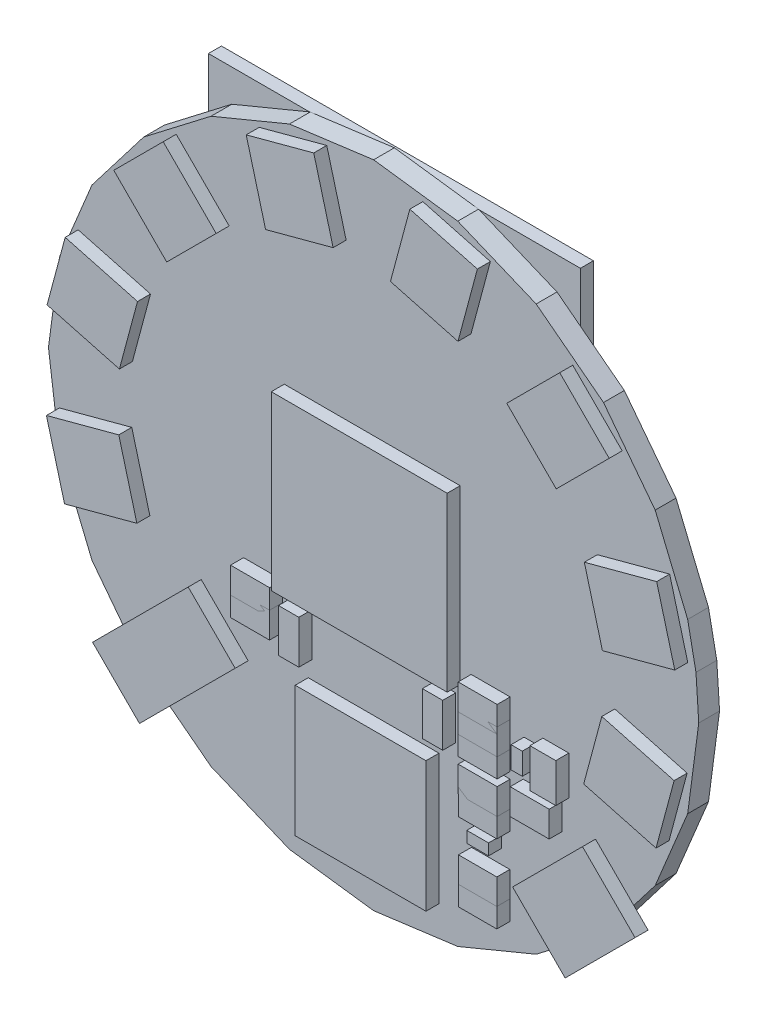
SolidWorks part; units mm, degrees
ref_plane "Plan de face" through (0, 0, 0) normal (0, 0, 1) x (1, 0, 0)
ref_plane "Plan de dessus" through (0, 0, 0) normal (0, 1, 0) x (1, 0, 0)
ref_plane "Plan de droite" through (0, 0, 0) normal (1, 0, 0) x (0, 0, -1)
sketch "Esquisse1" plane through (0, 0, 0) normal (0, 0, 1) x (1, 0, 0)
  line L0 (140.8, 53.6) -> (140.5861, 56.8632)
  line L1 (140.5861, 56.8632) -> (139.9481, 60.0705)
  line L2 (139.9481, 60.0705) -> (137.4506, 66.1)
  line L3 (137.4506, 66.1) -> (133.4777, 71.2777)
  line L4 (133.4777, 71.2777) -> (128.3, 75.2506)
  line L5 (128.3, 75.2506) -> (122.2705, 77.7481)
  line L6 (122.2705, 77.7481) -> (115.8, 78.6)
  line L7 (115.8, 78.6) -> (109.3295, 77.7481)
  line L8 (109.3295, 77.7481) -> (103.3, 75.2506)
  line L9 (103.3, 75.2506) -> (98.1223, 71.2777)
  line L10 (98.1223, 71.2777) -> (94.1494, 66.1)
  line L11 (94.1494, 66.1) -> (91.6519, 60.0705)
  line L12 (91.6519, 60.0705) -> (90.8, 53.6)
  line L13 (90.8, 53.6) -> (91.6519, 47.1295)
  line L14 (91.6519, 47.1295) -> (94.1494, 41.1)
  line L15 (94.1494, 41.1) -> (98.1223, 35.9223)
  line L16 (98.1223, 35.9223) -> (103.3, 31.9494)
  line L17 (103.3, 31.9494) -> (109.3295, 29.4519)
  line L18 (109.3295, 29.4519) -> (115.8, 28.6)
  line L19 (115.8, 28.6) -> (122.2705, 29.4519)
  line L20 (122.2705, 29.4519) -> (128.3, 31.9494)
  line L21 (128.3, 31.9494) -> (133.4777, 35.9223)
  line L22 (133.4777, 35.9223) -> (137.4506, 41.1)
  line L23 (137.4506, 41.1) -> (139.9481, 47.1295)
  line L24 (139.9481, 47.1295) -> (140.8, 53.6)
extrude "BOARD" add sketch "Esquisse1" along normal blind 1.6 separate body
ref_plane "Plan1" through (0, 0, 1.6) normal (0, 0, 1) x (1, 0, 0)
sketch "Esquisse2" plane through (0, 0, 1.6) normal (0, 0, 1) x (1, 0, 0)
  line L0 (91.6447, 49.9981) -> (97.2062, 51.4883)
  line L1 (97.2062, 51.4883) -> (98.5977, 46.2952)
  line L2 (98.5977, 46.2952) -> (93.0362, 44.805)
  line L3 (93.0362, 44.805) -> (91.6447, 49.9981)
extrude "WS2812B-1" add sketch "Esquisse2" along normal blind 1 separate body
sketch "Esquisse3" plane through (0, 0, 1.6) normal (0, 0, 1) x (1, 0, 0)
  line L0 (93.0853, 62.5782) -> (98.6468, 61.088)
  line L1 (98.6468, 61.088) -> (97.2553, 55.8949)
  line L2 (97.2553, 55.8949) -> (91.6938, 57.3851)
  line L3 (91.6938, 57.3851) -> (93.0853, 62.5782)
extrude "WS2812B-2" add sketch "Esquisse3" along normal blind 1 separate body
sketch "Esquisse4" plane through (0, 0, 1.6) normal (0, 0, 1) x (1, 0, 0)
  line L0 (100.6229, 72.7129) -> (104.6942, 68.6416)
  line L1 (104.6942, 68.6416) -> (100.8925, 64.8399)
  line L2 (100.8925, 64.8399) -> (96.8212, 68.9112)
  line L3 (96.8212, 68.9112) -> (100.6229, 72.7129)
extrude "WS2812B-3" add sketch "Esquisse4" along normal blind 1 separate body
sketch "Esquisse5" plane through (0, 0, 1.6) normal (0, 0, 1) x (1, 0, 0)
  line L0 (112.1981, 77.7553) -> (113.6883, 72.1938)
  line L1 (113.6883, 72.1938) -> (108.4952, 70.8023)
  line L2 (108.4952, 70.8023) -> (107.005, 76.3638)
  line L3 (107.005, 76.3638) -> (112.1981, 77.7553)
extrude "WS2812B-4" add sketch "Esquisse5" along normal blind 1 separate body
sketch "Esquisse6" plane through (0, 0, 1.6) normal (0, 0, 1) x (1, 0, 0)
  line L0 (124.7782, 76.3147) -> (123.288, 70.7532)
  line L1 (123.288, 70.7532) -> (118.0949, 72.1447)
  line L2 (118.0949, 72.1447) -> (119.5851, 77.7062)
  line L3 (119.5851, 77.7062) -> (124.7782, 76.3147)
extrude "WS2812B-5" add sketch "Esquisse6" along normal blind 1 separate body
sketch "Esquisse7" plane through (0, 0, 1.6) normal (0, 0, 1) x (1, 0, 0)
  line L0 (134.9129, 68.7771) -> (130.8416, 64.7058)
  line L1 (130.8416, 64.7058) -> (127.0399, 68.5075)
  line L2 (127.0399, 68.5075) -> (131.1112, 72.5788)
  line L3 (131.1112, 72.5788) -> (134.9129, 68.7771)
extrude "WS2812B-6" add sketch "Esquisse7" along normal blind 1 separate body
sketch "Esquisse8" plane through (0, 0, 1.6) normal (0, 0, 1) x (1, 0, 0)
  line L0 (139.9553, 57.2019) -> (134.3938, 55.7117)
  line L1 (134.3938, 55.7117) -> (133.0023, 60.9048)
  line L2 (133.0023, 60.9048) -> (138.5638, 62.395)
  line L3 (138.5638, 62.395) -> (139.9553, 57.2019)
extrude "WS2812B-7" add sketch "Esquisse8" along normal blind 1 separate body
sketch "Esquisse9" plane through (0, 0, 1.6) normal (0, 0, 1) x (1, 0, 0)
  line L0 (138.5147, 44.6218) -> (132.9532, 46.112)
  line L1 (132.9532, 46.112) -> (134.3447, 51.3051)
  line L2 (134.3447, 51.3051) -> (139.9062, 49.8149)
  line L3 (139.9062, 49.8149) -> (138.5147, 44.6218)
extrude "WS2812B-8" add sketch "Esquisse9" along normal blind 1 separate body
sketch "Esquisse10" plane through (0, 0, 0) normal (0, 0, 1) x (1, 0, 0)
  line L0 (130.1, 77.727) -> (101.5, 77.727)
  line L1 (101.5, 77.727) -> (101.5, 57.473)
  line L2 (101.5, 57.473) -> (130.1, 57.473)
  line L3 (130.1, 57.473) -> (130.1, 77.727)
extrude "3V_BAT_HOLDER-1" add sketch "Esquisse10" against normal blind 1 separate body
sketch "Esquisse11" plane through (0, 0, 1.6) normal (0, 0, 1) x (1, 0, 0)
  line L0 (123.3016, 42.6084) -> (126.2984, 42.6084)
  line L1 (126.2984, 42.6084) -> (126.2984, 40.617)
  line L2 (126.2984, 40.617) -> (123.3016, 40.617)
  line L3 (123.3016, 40.617) -> (123.3016, 42.6084)
extrude "C0603-1" add sketch "Esquisse11" along normal blind 1 separate body
sketch "Esquisse12" plane through (0, 0, 1.6) normal (0, 0, 1) x (1, 0, 0)
  line L0 (127.3016, 43.1084) -> (130.2984, 43.1084)
  line L1 (130.2984, 43.1084) -> (130.2984, 41.117)
  line L2 (130.2984, 41.117) -> (127.3016, 41.117)
  line L3 (127.3016, 41.117) -> (127.3016, 43.1084)
extrude "C0603-2" add sketch "Esquisse12" along normal blind 1 separate body
sketch "Esquisse13" plane through (0, 0, 1.6) normal (0, 0, 1) x (1, 0, 0)
  line L0 (123.3016, 45.1084) -> (126.2984, 45.1084)
  line L1 (126.2984, 45.1084) -> (126.2984, 43.117)
  line L2 (126.2984, 43.117) -> (123.3016, 43.117)
  line L3 (123.3016, 43.117) -> (123.3016, 45.1084)
extrude "C0603-3" add sketch "Esquisse13" along normal blind 1 separate body
sketch "Esquisse14" plane through (0, 0, 1.6) normal (0, 0, 1) x (1, 0, 0)
  line L0 (105.8016, 45.6084) -> (108.7984, 45.6084)
  line L1 (108.7984, 45.6084) -> (108.7984, 43.617)
  line L2 (108.7984, 43.617) -> (105.8016, 43.617)
  line L3 (105.8016, 43.617) -> (105.8016, 45.6084)
extrude "C0603-4" add sketch "Esquisse14" along normal blind 1 separate body
sketch "Esquisse15" plane through (0, 0, 1.6) normal (0, 0, 1) x (1, 0, 0)
  line L0 (130.8084, 46.5984) -> (130.8084, 43.6016)
  line L1 (130.8084, 43.6016) -> (128.817, 43.6016)
  line L2 (128.817, 43.6016) -> (128.817, 46.5984)
  line L3 (128.817, 46.5984) -> (130.8084, 46.5984)
extrude "C0603-5" add sketch "Esquisse15" along normal blind 1 separate body
sketch "Esquisse16" plane through (0, 0, 1.6) normal (0, 0, 1) x (1, 0, 0)
  line L0 (126.2984, 44.5916) -> (123.3016, 44.5916)
  line L1 (123.3016, 44.5916) -> (123.3016, 46.583)
  line L2 (123.3016, 46.583) -> (126.2984, 46.583)
  line L3 (126.2984, 46.583) -> (126.2984, 44.5916)
extrude "C0603-6" add sketch "Esquisse16" along normal blind 1 separate body
sketch "Esquisse17" plane through (0, 0, 1.6) normal (0, 0, 1) x (1, 0, 0)
  line L0 (105.8016, 47.1084) -> (108.7984, 47.1084)
  line L1 (108.7984, 47.1084) -> (108.7984, 45.117)
  line L2 (108.7984, 45.117) -> (105.8016, 45.117)
  line L3 (105.8016, 45.117) -> (105.8016, 47.1084)
extrude "C0603-7" add sketch "Esquisse17" along normal blind 1 separate body
sketch "Esquisse18" plane through (0, 0, 1.6) normal (0, 0, 1) x (1, 0, 0)
  line L0 (126.2984, 46.0916) -> (123.3016, 46.0916)
  line L1 (123.3016, 46.0916) -> (123.3016, 48.083)
  line L2 (123.3016, 48.083) -> (126.2984, 48.083)
  line L3 (126.2984, 48.083) -> (126.2984, 46.0916)
extrude "C0603-8" add sketch "Esquisse18" along normal blind 1 separate body
sketch "Esquisse19" plane through (0, 0, 0) normal (0, 0, 1) x (1, 0, 0)
  line L0 (130.8856, 42.8738) -> (132.7279, 42.8738)
  line L1 (132.7279, 42.8738) -> (132.7279, 44.3239)
  line L2 (132.7279, 44.3239) -> (130.8856, 44.3239)
  line L3 (130.8856, 44.3239) -> (130.8856, 42.8738)
extrude "C0805POL-1" add sketch "Esquisse19" against normal blind 1 separate body
sketch "Esquisse20" plane through (0, 0, 0) normal (0, 0, 1) x (1, 0, 0)
  line L0 (100.6916, 45.9984) -> (100.6916, 42.0016)
  line L1 (100.6916, 42.0016) -> (102.683, 42.0016)
  line L2 (102.683, 42.0016) -> (102.683, 45.9984)
  line L3 (102.683, 45.9984) -> (100.6916, 45.9984)
extrude "C0805-1" add sketch "Esquisse20" against normal blind 1 separate body
sketch "Esquisse21" plane through (0, 0, 0) normal (0, 0, 1) x (1, 0, 0)
  line L0 (99.5984, 45.6084) -> (95.6016, 45.6084)
  line L1 (95.6016, 45.6084) -> (95.6016, 43.617)
  line L2 (95.6016, 43.617) -> (99.5984, 43.617)
  line L3 (99.5984, 43.617) -> (99.5984, 45.6084)
extrude "C0805-2" add sketch "Esquisse21" against normal blind 1 separate body
sketch "Esquisse22" plane through (0, 0, 0) normal (0, 0, 1) x (1, 0, 0)
  line L0 (135.8084, 44.6016) -> (135.8084, 47.5984)
  line L1 (135.8084, 47.5984) -> (133.817, 47.5984)
  line L2 (133.817, 47.5984) -> (133.817, 44.6016)
  line L3 (133.817, 44.6016) -> (135.8084, 44.6016)
extrude "C0603-9" add sketch "Esquisse22" against normal blind 1 separate body
sketch "Esquisse23" plane through (0, 0, 0) normal (0, 0, 1) x (1, 0, 0)
  line L0 (111.8084, 45.6016) -> (111.8084, 48.5984)
  line L1 (111.8084, 48.5984) -> (109.817, 48.5984)
  line L2 (109.817, 48.5984) -> (109.817, 45.6016)
  line L3 (109.817, 45.6016) -> (111.8084, 45.6016)
extrude "C0603-10" add sketch "Esquisse23" against normal blind 1 separate body
sketch "Esquisse24" plane through (0, 0, 0) normal (0, 0, 1) x (1, 0, 0)
  line L0 (121.8084, 45.6016) -> (121.8084, 48.5984)
  line L1 (121.8084, 48.5984) -> (119.817, 48.5984)
  line L2 (119.817, 48.5984) -> (119.817, 45.6016)
  line L3 (119.817, 45.6016) -> (121.8084, 45.6016)
extrude "C0603-11" add sketch "Esquisse24" against normal blind 1 separate body
sketch "Esquisse25" plane through (0, 0, 0) normal (0, 0, 1) x (1, 0, 0)
  line L0 (123.5738, 48.0144) -> (123.5738, 46.1721)
  line L1 (123.5738, 46.1721) -> (125.0239, 46.1721)
  line L2 (125.0239, 46.1721) -> (125.0239, 48.0144)
  line L3 (125.0239, 48.0144) -> (123.5738, 48.0144)
extrude "C0805POL-2" add sketch "Esquisse25" against normal blind 1 separate body
sketch "Esquisse26" plane through (0, 0, 0) normal (0, 0, 1) x (1, 0, 0)
  line L0 (98.5144, 49.3262) -> (96.6721, 49.3262)
  line L1 (96.6721, 49.3262) -> (96.6721, 47.8761)
  line L2 (96.6721, 47.8761) -> (98.5144, 47.8761)
  line L3 (98.5144, 47.8761) -> (98.5144, 49.3262)
extrude "C0805POL-3" add sketch "Esquisse26" against normal blind 1 separate body
sketch "Esquisse27" plane through (0, 0, 0) normal (0, 0, 1) x (1, 0, 0)
  line L0 (128.7144, 49.3262) -> (126.8721, 49.3262)
  line L1 (126.8721, 49.3262) -> (126.8721, 47.8761)
  line L2 (126.8721, 47.8761) -> (128.7144, 47.8761)
  line L3 (128.7144, 47.8761) -> (128.7144, 49.3262)
extrude "C0805POL-4" add sketch "Esquisse27" against normal blind 1 separate body
sketch "Esquisse28" plane through (0, 0, 0) normal (0, 0, 1) x (1, 0, 0)
  line L0 (128.7144, 51.8262) -> (126.8721, 51.8262)
  line L1 (126.8721, 51.8262) -> (126.8721, 50.3761)
  line L2 (126.8721, 50.3761) -> (128.7144, 50.3761)
  line L3 (128.7144, 50.3761) -> (128.7144, 51.8262)
extrude "C0805POL-5" add sketch "Esquisse28" against normal blind 1 separate body
sketch "Esquisse29" plane through (0, 0, 0) normal (0, 0, 1) x (1, 0, 0)
  line L0 (134.3016, 50.5916) -> (137.2984, 50.5916)
  line L1 (137.2984, 50.5916) -> (137.2984, 52.583)
  line L2 (137.2984, 52.583) -> (134.3016, 52.583)
  line L3 (134.3016, 52.583) -> (134.3016, 50.5916)
extrude "C0603-12" add sketch "Esquisse29" against normal blind 1 separate body
sketch "Esquisse30" plane through (0, 0, 0) normal (0, 0, 1) x (1, 0, 0)
  line L0 (128.7144, 54.3262) -> (126.8721, 54.3262)
  line L1 (126.8721, 54.3262) -> (126.8721, 52.8761)
  line L2 (126.8721, 52.8761) -> (128.7144, 52.8761)
  line L3 (128.7144, 52.8761) -> (128.7144, 54.3262)
extrude "C0805POL-6" add sketch "Esquisse30" against normal blind 1 separate body
sketch "Esquisse31" plane through (0, 0, 0) normal (0, 0, 1) x (1, 0, 0)
  line L0 (100.1916, 56.5984) -> (100.1916, 52.6016)
  line L1 (100.1916, 52.6016) -> (102.183, 52.6016)
  line L2 (102.183, 52.6016) -> (102.183, 56.5984)
  line L3 (102.183, 56.5984) -> (100.1916, 56.5984)
extrude "C0805-3" add sketch "Esquisse31" against normal blind 1 separate body
sketch "Esquisse32" plane through (0, 0, 0) normal (0, 0, 1) x (1, 0, 0)
  line L0 (102.2916, 56.5984) -> (102.2916, 52.6016)
  line L1 (102.2916, 52.6016) -> (104.283, 52.6016)
  line L2 (104.283, 52.6016) -> (104.283, 56.5984)
  line L3 (104.283, 56.5984) -> (102.2916, 56.5984)
extrude "C0805-4" add sketch "Esquisse32" against normal blind 1 separate body
sketch "Esquisse33" plane through (0, 0, 0) normal (0, 0, 1) x (1, 0, 0)
  line L0 (108.3084, 52.6016) -> (108.3084, 56.5984)
  line L1 (108.3084, 56.5984) -> (106.317, 56.5984)
  line L2 (106.317, 56.5984) -> (106.317, 52.6016)
  line L3 (106.317, 52.6016) -> (108.3084, 52.6016)
extrude "C0805-5" add sketch "Esquisse33" against normal blind 1 separate body
sketch "Esquisse34" plane through (0, 0, 0) normal (0, 0, 1) x (1, 0, 0)
  line L0 (135.5262, 53.6856) -> (135.5262, 55.5279)
  line L1 (135.5262, 55.5279) -> (134.0761, 55.5279)
  line L2 (134.0761, 55.5279) -> (134.0761, 53.6856)
  line L3 (134.0761, 53.6856) -> (135.5262, 53.6856)
extrude "C0805POL-7" add sketch "Esquisse34" against normal blind 1 separate body
sketch "Esquisse35" plane through (0, 0, 0) normal (0, 0, 1) x (1, 0, 0)
  line L0 (117.2916, 59.0984) -> (117.2916, 56.1016)
  line L1 (117.2916, 56.1016) -> (119.283, 56.1016)
  line L2 (119.283, 56.1016) -> (119.283, 59.0984)
  line L3 (119.283, 59.0984) -> (117.2916, 59.0984)
extrude "C0603-13" add sketch "Esquisse35" against normal blind 1 separate body
sketch "Esquisse36" plane through (0, 0, 0) normal (0, 0, 1) x (1, 0, 0)
  line L0 (125.3084, 56.1016) -> (125.3084, 59.0984)
  line L1 (125.3084, 59.0984) -> (123.317, 59.0984)
  line L2 (123.317, 59.0984) -> (123.317, 56.1016)
  line L3 (123.317, 56.1016) -> (125.3084, 56.1016)
extrude "C0603-14" add sketch "Esquisse36" against normal blind 1 separate body
sketch "Esquisse37" plane through (0, 0, 0) normal (0, 0, 1) x (1, 0, 0)
  line L0 (127.5738, 62.5144) -> (127.5738, 60.6721)
  line L1 (127.5738, 60.6721) -> (129.0239, 60.6721)
  line L2 (129.0239, 60.6721) -> (129.0239, 62.5144)
  line L3 (129.0239, 62.5144) -> (127.5738, 62.5144)
extrude "C0805POL-8" add sketch "Esquisse37" against normal blind 1 separate body
sketch "Esquisse38" plane through (0, 0, 0) normal (0, 0, 1) x (1, 0, 0)
  line L0 (134.2984, 63.6084) -> (129.3016, 63.6084)
  line L1 (129.3016, 63.6084) -> (129.3016, 61.617)
  line L2 (129.3016, 61.617) -> (134.2984, 61.617)
  line L3 (134.2984, 61.617) -> (134.2984, 63.6084)
extrude "C1206-1" add sketch "Esquisse38" against normal blind 1 separate body
sketch "Esquisse39" plane through (0, 0, 0) normal (0, 0, 1) x (1, 0, 0)
  line L0 (126.6, 45.3865) -> (129, 45.3865)
  line L1 (129, 45.3865) -> (129, 46.75)
  line L2 (129, 46.75) -> (126.6, 46.75)
  line L3 (126.6, 46.75) -> (126.6, 45.3865)
extrude "SOD-323F-1" add sketch "Esquisse39" against normal blind 1 separate body
sketch "Esquisse40" plane through (0, 0, 0) normal (0, 0, 1) x (1, 0, 0)
  line L0 (137, 50.3135) -> (134.6, 50.3135)
  line L1 (134.6, 50.3135) -> (134.6, 48.95)
  line L2 (134.6, 48.95) -> (137, 48.95)
  line L3 (137, 48.95) -> (137, 50.3135)
extrude "SOD-323F-2" add sketch "Esquisse40" against normal blind 1 separate body
sketch "Esquisse41" plane through (0, 0, 0) normal (0, 0, 1) x (1, 0, 0)
  line L0 (130.6, 54.8865) -> (133, 54.8865)
  line L1 (133, 54.8865) -> (133, 56.25)
  line L2 (133, 56.25) -> (130.6, 56.25)
  line L3 (130.6, 56.25) -> (130.6, 54.8865)
extrude "SOD-323F-3" add sketch "Esquisse41" against normal blind 1 separate body
sketch "Esquisse42" plane through (0, 0, 0) normal (0, 0, 1) x (1, 0, 0)
  line L0 (135.5135, 57.9) -> (135.5135, 60.3)
  line L1 (135.5135, 60.3) -> (134.15, 60.3)
  line L2 (134.15, 60.3) -> (134.15, 57.9)
  line L3 (134.15, 57.9) -> (135.5135, 57.9)
extrude "SOD-323F-4" add sketch "Esquisse42" against normal blind 1 separate body
sketch "Esquisse43" plane through (0, 0, 0) normal (0, 0, 1) x (1, 0, 0)
  line L0 (129.2984, 44.6084) -> (126.3016, 44.6084)
  line L1 (126.3016, 44.6084) -> (126.3016, 42.617)
  line L2 (126.3016, 42.617) -> (129.2984, 42.617)
  line L3 (129.2984, 42.617) -> (129.2984, 44.6084)
extrude "0603-1" add sketch "Esquisse43" against normal blind 1 separate body
sketch "Esquisse44" plane through (0, 0, 0) normal (0, 0, 1) x (1, 0, 0)
  line L0 (130.15, 57.6) -> (133.45, 57.6)
  line L1 (133.45, 57.6) -> (133.45, 60.6)
  line L2 (133.45, 60.6) -> (130.15, 60.6)
  line L3 (130.15, 60.6) -> (130.15, 57.6)
extrude "SOT23-5-1" add sketch "Esquisse44" against normal blind 1 separate body
sketch "Esquisse45" plane through (0, 0, 1.6) normal (0, 0, 1) x (1, 0, 0)
  line L0 (95.1926, 36.6718) -> (102.5465, 44.0258)
  line L1 (102.5465, 44.0258) -> (106.1539, 40.4184)
  line L2 (106.1539, 40.4184) -> (98.8, 33.0645)
  line L3 (98.8, 33.0645) -> (95.1926, 36.6718)
extrude "STEREOJACK2_5MM-1" add sketch "Esquisse45" along normal blind 1 separate body
sketch "Esquisse46" plane through (0, 0, 0) normal (0, 0, 1) x (1, 0, 0)
  line L0 (112.2, 33) -> (119.4, 33)
  line L1 (119.4, 33) -> (119.4, 40.2)
  line L2 (119.4, 40.2) -> (112.2, 40.2)
  line L3 (112.2, 40.2) -> (112.2, 33)
extrude "LQFP32-08-1" add sketch "Esquisse46" against normal blind 1 separate body
sketch "Esquisse47" plane through (0, 0, 1.6) normal (0, 0, 1) x (1, 0, 0)
  line L0 (123.9618, 38.5318) -> (125.6382, 38.5318)
  line L1 (125.6382, 38.5318) -> (125.6382, 37.6678)
  line L2 (125.6382, 37.6678) -> (123.9618, 37.6678)
  line L3 (123.9618, 37.6678) -> (123.9618, 38.5318)
extrude "L0603-1" add sketch "Esquisse47" along normal blind 1 separate body
sketch "Esquisse48" plane through (0, 0, 1.6) normal (0, 0, 1) x (1, 0, 0)
  line L0 (127.3682, 44.2618) -> (127.3682, 45.9382)
  line L1 (127.3682, 45.9382) -> (128.2322, 45.9382)
  line L2 (128.2322, 45.9382) -> (128.2322, 44.2618)
  line L3 (128.2322, 44.2618) -> (127.3682, 44.2618)
extrude "L0603-2" add sketch "Esquisse48" along normal blind 1 separate body
sketch "Esquisse49" plane through (0, 0, 0) normal (0, 0, 1) x (1, 0, 0)
  line L0 (98.4382, 47.0318) -> (96.7618, 47.0318)
  line L1 (96.7618, 47.0318) -> (96.7618, 46.1678)
  line L2 (96.7618, 46.1678) -> (98.4382, 46.1678)
  line L3 (98.4382, 46.1678) -> (98.4382, 47.0318)
extrude "L0603-3" add sketch "Esquisse49" against normal blind 1 separate body
sketch "Esquisse50" plane through (0, 0, 0) normal (0, 0, 1) x (1, 0, 0)
  line L0 (98.4382, 51.0318) -> (96.7618, 51.0318)
  line L1 (96.7618, 51.0318) -> (96.7618, 50.1678)
  line L2 (96.7618, 50.1678) -> (98.4382, 50.1678)
  line L3 (98.4382, 50.1678) -> (98.4382, 51.0318)
extrude "L0603-4" add sketch "Esquisse50" against normal blind 1 separate body
sketch "Esquisse51" plane through (0, 0, 0) normal (0, 0, 1) x (1, 0, 0)
  line L0 (112.8682, 58.4382) -> (112.8682, 56.7618)
  line L1 (112.8682, 56.7618) -> (113.7322, 56.7618)
  line L2 (113.7322, 56.7618) -> (113.7322, 58.4382)
  line L3 (113.7322, 58.4382) -> (112.8682, 58.4382)
extrude "L0603-5" add sketch "Esquisse51" against normal blind 1 separate body
sketch "Esquisse52" plane through (0, 0, 0) normal (0, 0, 1) x (1, 0, 0)
  circle A0 centre (115.8, 53.6) radius 3
  dimension "D1" = 6
  dimension "D2" = 0
  dimension "D3" = 0
extrude "F6050AP-1" add sketch "Esquisse52" against normal blind 1 separate body
sketch "Esquisse53" plane through (0, 0, 0) normal (0, 0, 1) x (1, 0, 0)
  line L0 (102.7224, 62.8954) -> (99.8014, 62.8954)
  line L1 (99.8014, 62.8954) -> (99.8014, 60.3046)
  line L2 (99.8014, 60.3046) -> (102.7224, 60.3046)
  line L3 (102.7224, 60.3046) -> (102.7224, 62.8954)
extrude "SOT23-1" add sketch "Esquisse53" against normal blind 1 separate body
sketch "Esquisse54" plane through (0, 0, 1.6) normal (0, 0, 1) x (1, 0, 0)
  line L0 (123.327, 35.083) -> (126.273, 35.083)
  line L1 (126.273, 35.083) -> (126.273, 33.117)
  line L2 (126.273, 33.117) -> (123.327, 33.117)
  line L3 (123.327, 33.117) -> (123.327, 35.083)
extrude "R0603-1" add sketch "Esquisse54" along normal blind 1 separate body
sketch "Esquisse55" plane through (0, 0, 1.6) normal (0, 0, 1) x (1, 0, 0)
  line L0 (123.327, 36.583) -> (126.273, 36.583)
  line L1 (126.273, 36.583) -> (126.273, 34.617)
  line L2 (126.273, 34.617) -> (123.327, 34.617)
  line L3 (123.327, 34.617) -> (123.327, 36.583)
extrude "R0603-2" add sketch "Esquisse55" along normal blind 1 separate body
sketch "Esquisse56" plane through (0, 0, 1.6) normal (0, 0, 1) x (1, 0, 0)
  line L0 (123.327, 41.083) -> (126.273, 41.083)
  line L1 (126.273, 41.083) -> (126.273, 39.117)
  line L2 (126.273, 39.117) -> (123.327, 39.117)
  line L3 (123.327, 39.117) -> (123.327, 41.083)
extrude "R0603-3" add sketch "Esquisse56" along normal blind 1 separate body
sketch "Esquisse57" plane through (0, 0, 0) normal (0, 0, 1) x (1, 0, 0)
  line L0 (104.383, 33.927) -> (104.383, 36.873)
  line L1 (104.383, 36.873) -> (102.417, 36.873)
  line L2 (102.417, 36.873) -> (102.417, 33.927)
  line L3 (102.417, 33.927) -> (104.383, 33.927)
extrude "R0603-4" add sketch "Esquisse57" against normal blind 1 separate body
sketch "Esquisse58" plane through (0, 0, 0) normal (0, 0, 1) x (1, 0, 0)
  line L0 (106.183, 33.927) -> (106.183, 36.873)
  line L1 (106.183, 36.873) -> (104.217, 36.873)
  line L2 (104.217, 36.873) -> (104.217, 33.927)
  line L3 (104.217, 33.927) -> (106.183, 33.927)
extrude "R0603-5" add sketch "Esquisse58" against normal blind 1 separate body
sketch "Esquisse59" plane through (0, 0, 0) normal (0, 0, 1) x (1, 0, 0)
  line L0 (112.327, 47.117) -> (115.273, 47.117)
  line L1 (115.273, 47.117) -> (115.273, 49.083)
  line L2 (115.273, 49.083) -> (112.327, 49.083)
  line L3 (112.327, 49.083) -> (112.327, 47.117)
extrude "R0603-6" add sketch "Esquisse59" against normal blind 1 separate body
sketch "Esquisse60" plane through (0, 0, 0) normal (0, 0, 1) x (1, 0, 0)
  line L0 (119.273, 49.083) -> (116.327, 49.083)
  line L1 (116.327, 49.083) -> (116.327, 47.117)
  line L2 (116.327, 47.117) -> (119.273, 47.117)
  line L3 (119.273, 47.117) -> (119.273, 49.083)
extrude "R0603-7" add sketch "Esquisse60" against normal blind 1 separate body
sketch "Esquisse61" plane through (0, 0, 0) normal (0, 0, 1) x (1, 0, 0)
  line L0 (106.283, 53.127) -> (106.283, 56.073)
  line L1 (106.283, 56.073) -> (104.317, 56.073)
  line L2 (104.317, 56.073) -> (104.317, 53.127)
  line L3 (104.317, 53.127) -> (106.283, 53.127)
extrude "R0603-8" add sketch "Esquisse61" against normal blind 1 separate body
sketch "Esquisse62" plane through (0, 0, 0) normal (0, 0, 1) x (1, 0, 0)
  line L0 (135.817, 56.073) -> (135.817, 53.127)
  line L1 (135.817, 53.127) -> (137.783, 53.127)
  line L2 (137.783, 53.127) -> (137.783, 56.073)
  line L3 (137.783, 56.073) -> (135.817, 56.073)
extrude "R0603-9" add sketch "Esquisse62" against normal blind 1 separate body
sketch "Esquisse63" plane through (0, 0, 0) normal (0, 0, 1) x (1, 0, 0)
  line L0 (121.283, 56.127) -> (121.283, 59.073)
  line L1 (121.283, 59.073) -> (119.317, 59.073)
  line L2 (119.317, 59.073) -> (119.317, 56.127)
  line L3 (119.317, 56.127) -> (121.283, 56.127)
extrude "R0603-10" add sketch "Esquisse63" against normal blind 1 separate body
sketch "Esquisse64" plane through (0, 0, 0) normal (0, 0, 1) x (1, 0, 0)
  line L0 (121.317, 59.073) -> (121.317, 56.127)
  line L1 (121.317, 56.127) -> (123.283, 56.127)
  line L2 (123.283, 56.127) -> (123.283, 59.073)
  line L3 (123.283, 59.073) -> (121.317, 59.073)
extrude "R0603-11" add sketch "Esquisse64" against normal blind 1 separate body
sketch "Esquisse65" plane through (0, 0, 0) normal (0, 0, 1) x (1, 0, 0)
  line L0 (127.283, 56.127) -> (127.283, 59.073)
  line L1 (127.283, 59.073) -> (125.317, 59.073)
  line L2 (125.317, 59.073) -> (125.317, 56.127)
  line L3 (125.317, 56.127) -> (127.283, 56.127)
extrude "R0603-12" add sketch "Esquisse65" against normal blind 1 separate body
sketch "Esquisse66" plane through (0, 0, 0) normal (0, 0, 1) x (1, 0, 0)
  line L0 (127.317, 59.073) -> (127.317, 56.127)
  line L1 (127.317, 56.127) -> (129.283, 56.127)
  line L2 (129.283, 56.127) -> (129.283, 59.073)
  line L3 (129.283, 59.073) -> (127.317, 59.073)
extrude "R0603-13" add sketch "Esquisse66" against normal blind 1 separate body
sketch "Esquisse67" plane through (0, 0, 0) normal (0, 0, 1) x (1, 0, 0)
  line L0 (99.827, 57.117) -> (102.773, 57.117)
  line L1 (102.773, 57.117) -> (102.773, 59.083)
  line L2 (102.773, 59.083) -> (99.827, 59.083)
  line L3 (99.827, 59.083) -> (99.827, 57.117)
extrude "R0603-14" add sketch "Esquisse67" against normal blind 1 separate body
sketch "Esquisse68" plane through (0, 0, 0) normal (0, 0, 1) x (1, 0, 0)
  line L0 (135.817, 60.573) -> (135.817, 57.627)
  line L1 (135.817, 57.627) -> (137.783, 57.627)
  line L2 (137.783, 57.627) -> (137.783, 60.573)
  line L3 (137.783, 60.573) -> (135.817, 60.573)
extrude "R0603-15" add sketch "Esquisse68" against normal blind 1 separate body
sketch "Esquisse69" plane through (0, 0, 0) normal (0, 0, 1) x (1, 0, 0)
  line L0 (122.9665, 35.6635) -> (122.9665, 31.6122)
  line L1 (122.9665, 31.6122) -> (125.6335, 31.6122)
  line L2 (125.6335, 31.6122) -> (125.6335, 35.6635)
  line L3 (125.6335, 35.6635) -> (122.9665, 35.6635)
extrude "157SW-1" add sketch "Esquisse69" against normal blind 1 separate body
sketch "Esquisse70" plane through (0, 0, 0) normal (0, 0, 1) x (1, 0, 0)
  line L0 (92.7106, 58.1) -> (98.8635, 58.1)
  line L1 (98.8635, 58.1) -> (98.8635, 63.1635)
  line L2 (98.8635, 63.1635) -> (92.7106, 63.1635)
  line L3 (92.7106, 63.1635) -> (92.7106, 58.1)
extrude "SMT-0540-S-R-1" add sketch "Esquisse70" against normal blind 1 separate body
sketch "Esquisse71" plane through (0, 0, 1.6) normal (0, 0, 1) x (1, 0, 0)
  line L0 (108.9331, 60.225) -> (122.4531, 60.225)
  line L1 (122.4531, 60.225) -> (122.4531, 46.975)
  line L2 (122.4531, 46.975) -> (108.9331, 46.975)
  line L3 (108.9331, 46.975) -> (108.9331, 60.225)
  line L5 (140.8, 53.6) -> (140.5861, 56.8632) construction
  point P4 (115.6931, 60.225)
  point P5 (122.4531, 53.6)
  point P8 (140.6987, 55.1449)
  point P9 (140.6931, 55.2316)
  dimension "D1" = 13.25
  dimension "D2" = 25
  dimension "D3" = 25
extrude "ENCODER_LED_3_KIT-1" add sketch "Esquisse71" along normal blind 1 separate body
sketch "Esquisse72" plane through (0, 0, 0) normal (0, 0, 1) x (1, 0, 0)
  line L0 (130.378, 45.6) -> (133.2982, 45.6)
  line L1 (133.2982, 45.6) -> (133.2982, 48.6)
  line L2 (133.2982, 48.6) -> (130.378, 48.6)
  line L3 (130.378, 48.6) -> (130.378, 45.6)
extrude "SOT23-DBV-1" add sketch "Esquisse72" against normal blind 1 separate body
sketch "Esquisse73" plane through (0, 0, 0) normal (0, 0, 1) x (1, 0, 0)
  line L0 (100.673, 45.973) -> (106.5, 45.973)
  line L1 (106.5, 45.973) -> (106.5, 51.8)
  line L2 (106.5, 51.8) -> (100.673, 51.8)
  line L3 (100.673, 51.8) -> (100.673, 45.973)
extrude "QFN-32-5MM-1" add sketch "Esquisse73" against normal blind 1 separate body
sketch "Esquisse74" plane through (0, 0, 0) normal (0, 0, 1) x (1, 0, 0)
  line L0 (130.35, 50.6) -> (133.3236, 50.6)
  line L1 (133.3236, 50.6) -> (133.3236, 53.6)
  line L2 (133.3236, 53.6) -> (130.35, 53.6)
  line L3 (130.35, 53.6) -> (130.35, 50.6)
extrude "SOT23-6-1" add sketch "Esquisse74" against normal blind 1 separate body
sketch "Esquisse75" plane through (0, 0, 1.6) normal (0, 0, 1) x (1, 0, 0)
  line L0 (120.825, 31.575) -> (110.775, 31.575)
  line L1 (110.775, 31.575) -> (110.775, 41.6)
  line L2 (110.775, 41.6) -> (120.825, 41.6)
  line L3 (120.825, 41.6) -> (120.825, 31.575)
extrude "LQFP64-05-1" add sketch "Esquisse75" along normal blind 1 separate body
sketch "Esquisse76" plane through (0, 0, 1.6) normal (0, 0, 1) x (1, 0, 0)
  line L0 (131.5284, 32.4821) -> (127.488, 36.5224)
  line L1 (127.488, 36.5224) -> (132.862, 41.8965)
  line L2 (132.862, 41.8965) -> (136.9024, 37.8561)
  line L3 (136.9024, 37.8561) -> (131.5284, 32.4821)
extrude "USB_MICRO_TG-1" add sketch "Esquisse76" along normal blind 1 separate body
sketch "Esquisse77" plane through (0, 0, 1.6) normal (0, 0, 1) x (1, 0, 0)
  line L0 (109.4865, 42.9365) -> (109.4865, 46.2635)
  line L1 (109.4865, 46.2635) -> (111.05, 46.2635)
  line L2 (111.05, 46.2635) -> (111.05, 42.9365)
  line L3 (111.05, 42.9365) -> (109.4865, 42.9365)
extrude "CRYSTAL-SMD-3_2X1_5MM-1" add sketch "Esquisse77" along normal blind 1 separate body
sketch "Esquisse78" plane through (0, 0, 1.6) normal (0, 0, 1) x (1, 0, 0)
  line L0 (122.1135, 46.2635) -> (122.1135, 42.9365)
  line L1 (122.1135, 42.9365) -> (120.55, 42.9365)
  line L2 (120.55, 42.9365) -> (120.55, 46.2635)
  line L3 (120.55, 46.2635) -> (122.1135, 46.2635)
extrude "CRYSTAL-SMD-3_2X1_5MM-2" add sketch "Esquisse78" along normal blind 1 separate body
